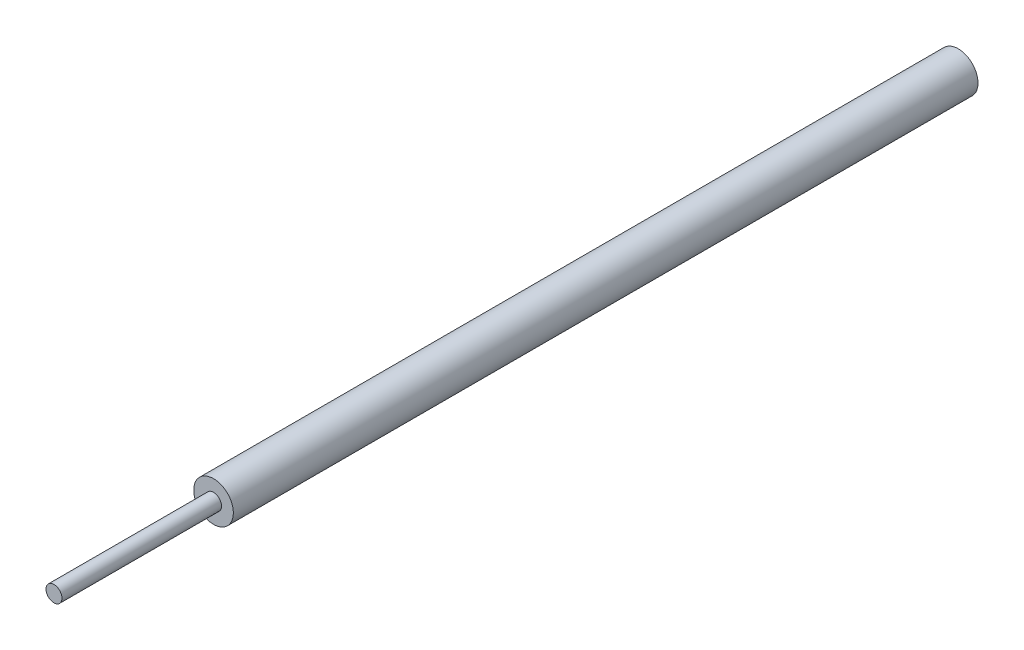
SolidWorks part; units mm, degrees
ref_plane "Front Plane" through (0, 0, 0) normal (0, 0, 1) x (1, 0, 0)
ref_plane "Top Plane" through (0, 0, 0) normal (0, 1, 0) x (1, 0, 0)
ref_plane "Right Plane" through (0, 0, 0) normal (1, 0, 0) x (0, 0, -1)
sketch "Sketch1" plane through (0, 0, 0) normal (0, 0, 1) x (1, 0, 0)
  circle A0 centre (0, 0) radius 3.725
  dimension "D1" = 7.45
extrude "Boss-Extrude1" add sketch "Sketch1" along normal blind 140
sketch "Sketch2" plane through (0, 0, 140) normal (0, 0, 1) x (1, 0, 0)
  circle A0 centre (0, 0) radius 1.5
  dimension "D1" = 3
extrude "Boss-Extrude2" add sketch "Sketch2" along normal blind 30
